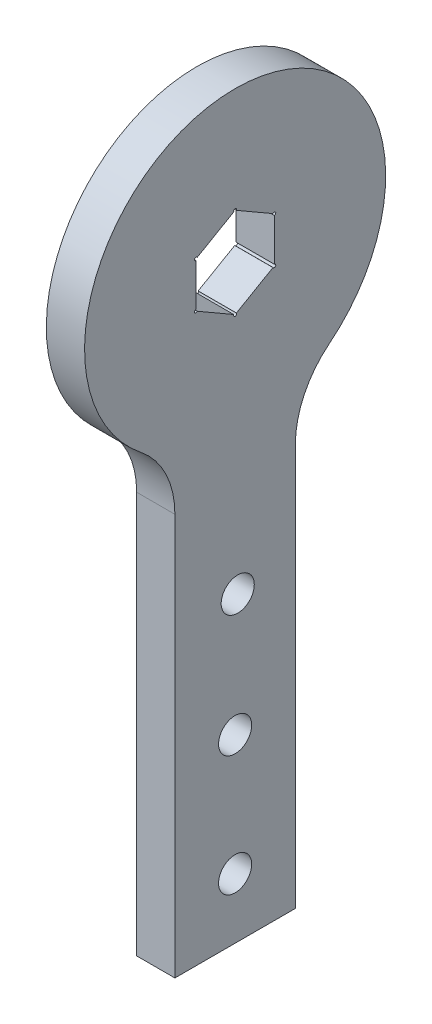
SolidWorks part; units mm, degrees
ref_plane "Front Plane" through (0, 0, 0) normal (0, 0, 1) x (1, 0, 0)
ref_plane "Top Plane" through (0, 0, 0) normal (0, 1, 0) x (1, 0, 0)
ref_plane "Right Plane" through (0, 0, 0) normal (1, 0, 0) x (0, 0, -1)
sketch "Sketch1" plane through (0, 0, 0) normal (1, 0, 0) x (0, 0, -1)
  line L0 (-10, -22.9129) -> (-10, -97.9129)
  line L1 (-10, -97.9129) -> (10, -97.9129)
  line L2 (10, -97.9129) -> (10, -22.9129)
  line L3 (-10, -22.9129) -> (10, -22.9129) construction
  arc A2 (10, -22.9129) -> (-10, -22.9129) centre (0, 0) ccw
  point P8 (0, -22.9129)
  dimension "D4" = 25
  dimension "D1" = 20
  dimension "D2" = 75
extrude "Boss-Extrude1" add sketch "Sketch1" along normal blind 6.35
sketch "Sketch2" plane through (6.35, 0, 0) normal (1, 0, 0) x (0, 0, -1)
  line L1 (-10, -97.9129) -> (10, -97.9129) construction
  circle A1 centre (0, -87.9129) radius 2.75
  circle A2 centre (0, -67.9129) radius 2.75
  circle A3 centre (0.4312, -47.9129) radius 2.75
  dimension "D1" = 20
  dimension "D2" = 5.5
  dimension "D3" = 5.5
  dimension "D4" = 10
  dimension "D8" = 5.5
  dimension "D6" = 20
extrude "Cut-Extrude1" cut sketch "Sketch2" against normal through all
fillet "Fillet1" radius 15 2 edges at (3.175, -22.9129, -10) (3.175, -22.9129, 10)
sketch "Sketch3" plane through (6.35, 0, 0) normal (1, 0, 0) x (0, 0, -1)
  line L1 (0, -7.5056) -> (6.5, -3.7528)
  line L2 (6.5, -3.7528) -> (6.5, 3.7528)
  line L3 (6.5, 3.7528) -> (0, 7.5056)
  line L4 (0, 7.5056) -> (-6.5, 3.7528)
  line L5 (-6.5, 3.7528) -> (-6.5, -3.7528)
  line L6 (-6.5, -3.7528) -> (0, -7.5056)
  circle A0 centre (0, 0) radius 6.5 construction
  dimension "D1" = 13
extrude "Cut-Extrude2" cut sketch "Sketch3" against normal up to next
sketch "Sketch4" plane through (6.35, 0, 0) normal (1, 0, 0) x (0, 0, -1)
  circle A0 centre (0, 7.5056) radius 0.25
  circle A1 centre (6.5, 3.7528) radius 0.25
  circle A2 centre (6.5, -3.7528) radius 0.25
  circle A3 centre (0, -7.5056) radius 0.25
  circle A4 centre (-6.5, -3.7528) radius 0.25
  circle A5 centre (-6.5, 3.7528) radius 0.25
  point P16 (0, 0)
extrude "Cut-Extrude3" cut sketch "Sketch4" against normal up to next
